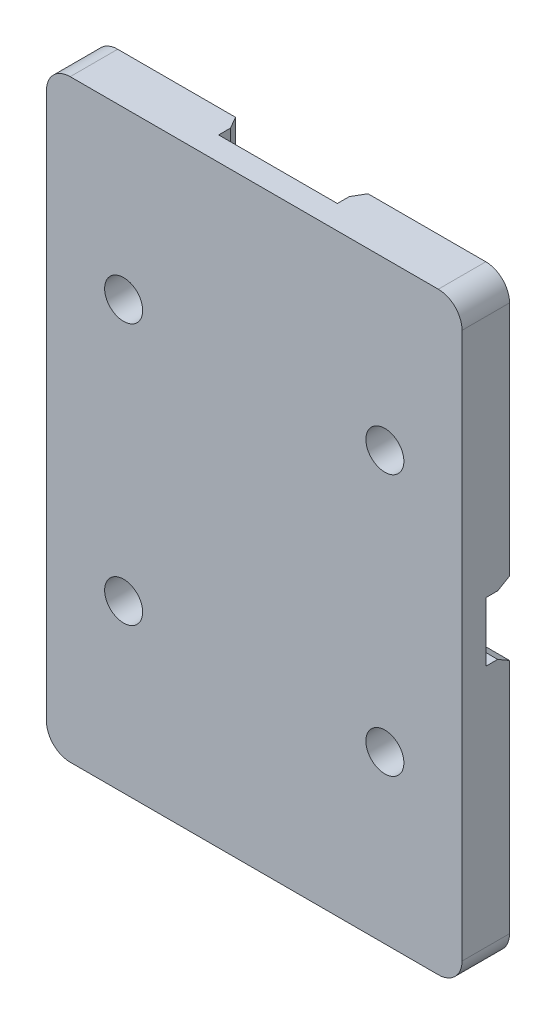
SolidWorks part; units mm, degrees
ref_plane "Piano frontale" through (0, 0, 0) normal (0, 0, 1) x (1, 0, 0)
ref_plane "Piano superiore" through (0, 0, 0) normal (0, 1, 0) x (1, 0, 0)
ref_plane "Piano destro" through (0, 0, 0) normal (1, 0, 0) x (0, 0, -1)
sketch "Schizzo1" plane through (0, 0, 0) normal (0, 0, 1) x (1, 0, 0)
  line L1 (-17.5, -25) -> (17.5, -25)
  line L2 (-17.5, -25) -> (-17.5, 25)
  line L3 (-17.5, 25) -> (17.5, 25)
  line L4 (17.5, -25) -> (17.5, 25)
  line L5 (-17.5, -25) -> (17.5, 25) construction
  line L6 (-17.5, 25) -> (17.5, -25) construction
  point P0 (0, 0)
  dimension "D1" = 35
  dimension "D2" = 50
extrude "Estrusione-Estrusione1" add sketch "Schizzo1" along normal mid plane 4 contours L3 L4 L1 L2
sketch "Schizzo2" plane through (0, 0, -2) normal (0, 0, -1) x (-1, 0, 0)
  line L0 (17.5, 25) -> (-17.5, 25) construction
  line L1 (-5, -25) -> (5, -25)
  line L2 (-5, -25) -> (-5, -2.5)
  line L3 (-5, 25) -> (5, 25)
  line L4 (5, -25) -> (5, -2.5)
  line L7 (17.5, -25) -> (17.5, 25) construction
  line L8 (-17.5, 2.5) -> (-5, 2.5)
  line L9 (-17.5, 2.5) -> (-17.5, -2.5)
  line L10 (-17.5, -2.5) -> (-5, -2.5)
  line L11 (17.5, 2.5) -> (17.5, -2.5)
  line L14 (5, 2.5) -> (17.5, 2.5)
  line L15 (5, 2.5) -> (5, 25)
  line L19 (-5, 2.5) -> (-5, 25)
  line L22 (5, -2.5) -> (17.5, -2.5)
  point P0 (0, 0)
  point P8 (0, 0)
  dimension "D1" = 10
  dimension "D2" = 5
extrude "Taglio-Estrusione1" cut sketch "Schizzo2" against normal blind 2
fillet "Raccordo1" radius 2 8 edges at (17.5, -25, 0) (-17.5, 25, 0) (-17.5, -25, 0) (-5, 2.5, -1) (-5, -2.5, -1) (5, -2.5, -1) (5, 2.5, -1) (17.5, 25, 0)
chamfer "Smusso1" distance 1 angle 30 12 edges at (-5, 14.75, -2) (-5.5858, 3.0858, -2) (-12.25, 2.5, -2) (-12.25, -2.5, -2) (-5.5858, -3.0858, -2) (-5, -14.75, -2) (5, -14.75, -2) (5.5858, -3.0858, -2) (12.25, -2.5, -2) (12.25, 2.5, -2) (5.5858, 3.0858, -2) (5, 14.75, -2)
sketch "Sketch1" plane through (0, 0, 2) normal (0, 0, 1) x (1, 0, 0)
  line L0 (0, 25) -> (0, -25) construction
  line L1 (-15.5, 25) -> (15.5, 25) construction
  line L2 (-15.5, -25) -> (15.5, -25) construction
  line L3 (17.5, -23) -> (17.5, 23) construction
  line L4 (17.5, 0) -> (-17.5, 0) construction
  line L5 (-17.5, -23) -> (-17.5, 23) construction
  circle A0 centre (-11, 11) radius 1.6
  circle A1 centre (11, 11) radius 1.6
  circle A2 centre (11, -11) radius 1.6
  circle A3 centre (-11, -11) radius 1.6
  dimension "D1" = 11
  dimension "D2" = 11
extrude "Cut-Extrude1" cut sketch "Sketch1" against normal through all both and the other way through all
ref_point "Point1"
